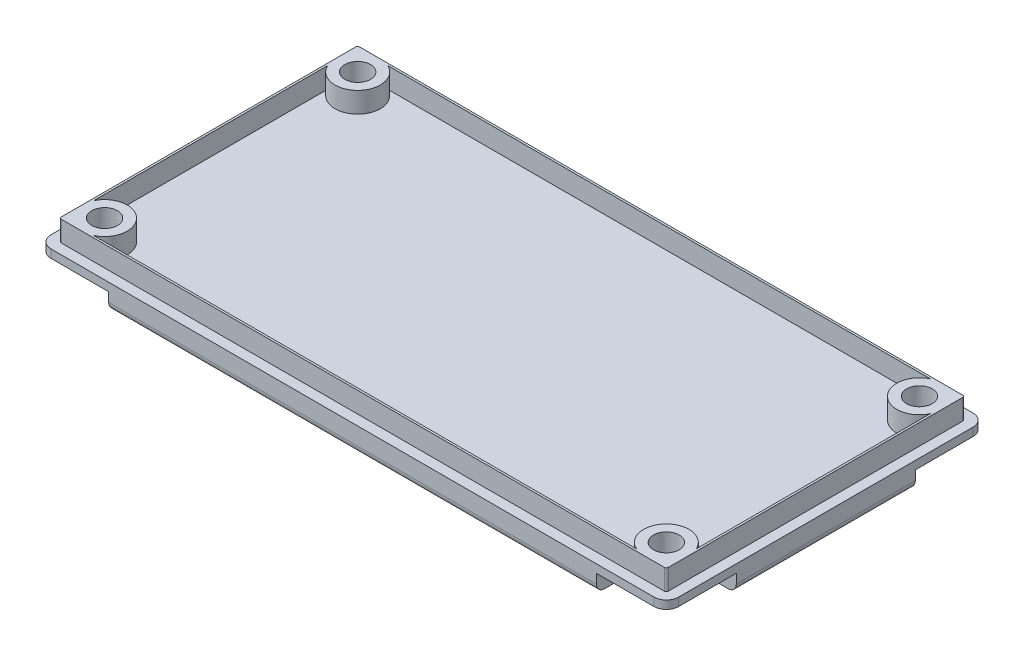
SolidWorks part; units mm, degrees
material "ABS"
ref_plane "Front Plane" through (0, 0, 0) normal (0, 0, 1) x (1, 0, 0)
ref_plane "Top Plane" through (0, 0, 0) normal (0, 1, 0) x (1, 0, 0)
ref_plane "Right Plane" through (0, 0, 0) normal (1, 0, 0) x (0, 0, -1)
sketch "Sketch1" plane through (0, 0, 0) normal (0, 1, 0) x (1, 0, 0)
  line L0 (-19.3675, 0) -> (19.3675, 0) construction
  line L1 (-18.6055, 9.8425) -> (18.6055, 9.8425)
  line L2 (-19.3675, 9.0805) -> (-19.3675, -9.0805)
  line L3 (-18.6055, -9.8425) -> (18.6055, -9.8425)
  line L4 (19.3675, 9.0805) -> (19.3675, -9.0805)
  line L5 (0, -9.8425) -> (0, 9.8425) construction
  line L8 (19.3675, 9.0805) -> (19.3675, -9.0805) construction
  line L9 (18.6055, -9.8425) -> (-18.6055, -9.8425) construction
  arc A0 (-18.6055, -9.8425) -> (-19.3675, -9.0805) centre (-18.6055, -9.0805) cw
  arc A1 (18.6055, -9.8425) -> (19.3675, -9.0805) centre (18.6055, -9.0805) ccw
  arc A2 (19.3675, 9.0805) -> (18.6055, 9.8425) centre (18.6055, 9.0805) ccw
  arc A3 (-19.3675, 9.0805) -> (-18.6055, 9.8425) centre (-18.6055, 9.0805) cw
  circle A4 centre (-17.3355, 7.8105) radius 0.7937
  circle A5 centre (17.3355, 7.8105) radius 0.7937
  circle A6 centre (17.3355, -7.8105) radius 0.7937
  circle A7 centre (-17.3355, -7.8105) radius 0.7937
  arc A9 (-19.3675, -9.0805) -> (-18.6055, -9.8425) centre (-18.6055, -9.0805) ccw construction
  circle A10 centre (17.3355, -7.8105) radius 0.7937 construction
extrude "Extrude1" add sketch "Sketch1" along normal blind 1.5875
fillet "Fillet2" radius 0.508 8 edges at (-19.3675, 0, 0) (-19.1443, 0, -9.6193) (0, 0, -9.8425) (19.1443, 0, -9.6193) (19.3675, 0, 0) (19.1443, 0, 9.6193) (0, 0, 9.8425) (-19.1443, 0, 9.6193)
sketch "Sketch2" plane through (0, 1.5875, 0) normal (0, 1, 0) x (-1, 0, 0)
  line L4 (-18.6055, -7.2285) -> (-18.6055, 7.2285)
  line L5 (-16.7535, 9.0805) -> (16.7535, 9.0805)
  line L6 (18.6055, 7.2285) -> (18.6055, -7.2285)
  line L7 (16.7535, -9.0805) -> (-16.7535, -9.0805)
  line L8 (18.6055, 9.2075) -> (-18.6055, 9.2075)
  line L9 (-18.7325, 9.0805) -> (-18.7325, -9.0805)
  line L10 (-18.6055, -9.2075) -> (18.6055, -9.2075)
  line L11 (18.7325, -9.0805) -> (18.7325, 9.0805)
  line L12 (18.6055, 9.2075) -> (-18.6055, 9.2075)
  line L13 (-18.7325, 9.0805) -> (-18.7325, -9.0805)
  line L14 (-18.6055, -9.2075) -> (18.6055, -9.2075)
  line L15 (18.7325, -9.0805) -> (18.7325, 9.0805)
  circle A4 centre (-17.3355, 7.8105) radius 0.7938 construction
  circle A5 centre (-17.3355, -7.8105) radius 0.7937 construction
  circle A6 centre (17.3355, -7.8105) radius 0.7937 construction
  circle A7 centre (17.3355, 7.8105) radius 0.7938 construction
  arc A8 (18.7325, 9.0805) -> (18.6055, 9.2075) centre (18.6055, 9.0805) ccw
  arc A9 (-18.6055, 9.2075) -> (-18.7325, 9.0805) centre (-18.6055, 9.0805) ccw
  arc A10 (-18.7325, -9.0805) -> (-18.6055, -9.2075) centre (-18.6055, -9.0805) ccw
  arc A11 (18.6055, -9.2075) -> (18.7325, -9.0805) centre (18.6055, -9.0805) ccw
  arc A12 (18.7325, 9.0805) -> (18.6055, 9.2075) centre (18.6055, 9.0805) ccw
  arc A13 (-18.6055, 9.2075) -> (-18.7325, 9.0805) centre (-18.6055, 9.0805) ccw
  arc A14 (-18.7325, -9.0805) -> (-18.6055, -9.2075) centre (-18.6055, -9.0805) ccw
  arc A15 (18.6055, -9.2075) -> (18.7325, -9.0805) centre (18.6055, -9.0805) ccw
  circle A16 centre (-17.3355, 7.8105) radius 0.7937
  circle A17 centre (-17.3355, -7.8105) radius 0.7937
  circle A18 centre (17.3355, -7.8105) radius 0.7937
  circle A19 centre (17.3355, 7.8105) radius 0.7937
  arc A20 (-16.7535, -9.0805) -> (-18.6055, -7.2285) centre (-17.3355, -7.8105) ccw
  arc A21 (16.7535, 9.0805) -> (18.6055, 7.2285) centre (17.3355, 7.8105) ccw
  arc A22 (18.6055, -7.2285) -> (16.7535, -9.0805) centre (17.3355, -7.8105) ccw
  arc A23 (-18.6055, 7.2285) -> (-16.7535, 9.0805) centre (-17.3355, 7.8105) ccw
  dimension "D1" = 0.635
extrude "Extrude2" add sketch "Sketch2" along normal blind 1.27
sketch "Sketch3" plane through (0, 0, 0) normal (0, -1, 0) x (1, 0, 0)
  line L0 (18.6055, -9.8425) -> (-18.6055, -9.8425) construction
  line L1 (-16.3195, -5.5245) -> (-19.3675, -5.5245)
  line L2 (-15.0495, -6.7945) -> (-15.0495, -9.8425)
  line L3 (-15.0495, -9.8425) -> (-19.3675, -9.8425)
  line L4 (-19.3675, -5.5245) -> (-19.3675, -9.8425)
  line L5 (-19.3675, -9.0805) -> (-19.3675, 9.0805) construction
  arc A1 (-15.0495, -6.7945) -> (-16.3195, -5.5245) centre (-16.3195, -6.7945) ccw
  point P10 (-15.0495, -5.5245)
  dimension "D1" = 1.27
  dimension "D2" = 4.318
extrude "Cut-Extrude1" cut sketch "Sketch3" against normal offset from surface 0.508 up to face at (0, 1.5875, 0)
mirror "Mirror1" about plane through (0, 0, 0) normal (1, 0, 0) of "Cut-Extrude1"
mirror "Mirror2" about plane through (0, 0, 0) normal (0, 0, 1) of "Cut-Extrude1", "Mirror1"
